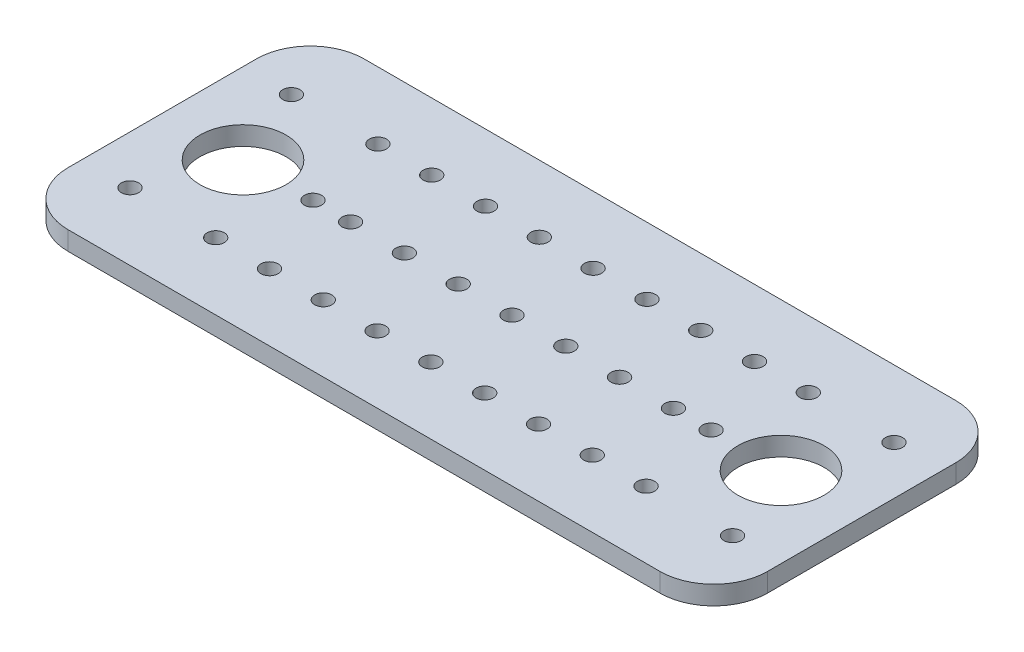
SolidWorks part; units mm, degrees
ref_plane "Front Plane" through (0, 0, 0) normal (0, 0, 1) x (1, 0, 0)
ref_plane "Top Plane" through (0, 0, 0) normal (0, 1, 0) x (1, 0, 0)
ref_plane "Right Plane" through (0, 0, 0) normal (1, 0, 0) x (0, 0, -1)
sketch "Sketch1" plane through (0, 0, 0) normal (0, 1, 0) x (1, 0, 0)
  line L0 (65, 20.185) -> (65, -60.6934) construction
  line L1 (0, 0) -> (130, 0)
  line L2 (0, 0) -> (0, -55)
  line L3 (0, -55) -> (130, -55)
  line L4 (130, 0) -> (130, -55)
  line L5 (-10.4412, -27.5) -> (139.8504, -27.5) construction
  circle A0 centre (9, -12.5) radius 1.6
  circle A1 centre (9, -42.5) radius 1.6
  circle A4 centre (121, -42.5) radius 1.6
  circle A7 centre (121, -12.5) radius 1.6
  circle A12 centre (15, -27.5) radius 8
  circle A13 centre (115, -27.5) radius 8
  circle A26 centre (65, -12.425) radius 1.6
  circle A27 centre (65, -42.575) radius 1.6
  circle A28 centre (75, -12.425) radius 1.6
  circle A29 centre (75, -42.575) radius 1.6
  circle A30 centre (85, -12.425) radius 1.6
  circle A31 centre (85, -42.575) radius 1.6
  circle A32 centre (95, -12.425) radius 1.6
  circle A33 centre (95, -42.575) radius 1.6
  circle A34 centre (105, -12.425) radius 1.6
  circle A35 centre (105, -42.575) radius 1.6
  circle A36 centre (55, -12.425) radius 1.6
  circle A37 centre (55, -42.575) radius 1.6
  circle A38 centre (45, -12.425) radius 1.6
  circle A39 centre (45, -42.575) radius 1.6
  circle A40 centre (35, -12.425) radius 1.6
  circle A41 centre (35, -42.575) radius 1.6
  circle A42 centre (25, -12.425) radius 1.6
  circle A43 centre (25, -42.575) radius 1.6
  circle A44 centre (65, -27.5) radius 1.6
  circle A45 centre (75, -27.5) radius 1.6
  circle A46 centre (85, -27.5) radius 1.6
  circle A47 centre (95, -27.5) radius 1.6
  circle A48 centre (55, -27.5) radius 1.6
  circle A49 centre (45, -27.5) radius 1.6
  circle A50 centre (35, -27.5) radius 1.6
  circle A51 centre (28, -27.5) radius 1.6
  circle A52 centre (102, -27.5) radius 1.6
  point P27 (65, -27.5)
  point P41 (65, -27.5)
  point P77 (27.2253, -27.5)
  point P78 (0, 0)
  point P79 (103.3914, -27.5)
  dimension "D3" = 3.2
  dimension "D4" = 3.2
  dimension "D5" = 30.15
  dimension "D6" = 3.2
  dimension "D13" = 5
  dimension "D14" = 5
  dimension "D15" = 3.2
  dimension "D16" = 4
  dimension "D25" = 16
  dimension "D27" = 16
  dimension "D8" = 3.2
  dimension "D9" = 15.075
  dimension "D17" = 4
  dimension "D18" = 3.2
  dimension "D19" = 3.2
  dimension "D1" = 130
  dimension "D2" = 55
  dimension "D7" = 30
  dimension "D10" = 0
  dimension "D11" = 65
  dimension "D12" = 9
  dimension "D20" = 37
  dimension "D21" = 37
  dimension "D26" = 15
  dimension "D28" = 15
extrude "Boss-Extrude4" add sketch "Sketch1" along normal blind 3.5
fillet "Fillet4" radius 10 4 edges at (0, 1.75, 0) (0, 1.75, 55) (130, 1.75, 55) (130, 1.75, 0)
